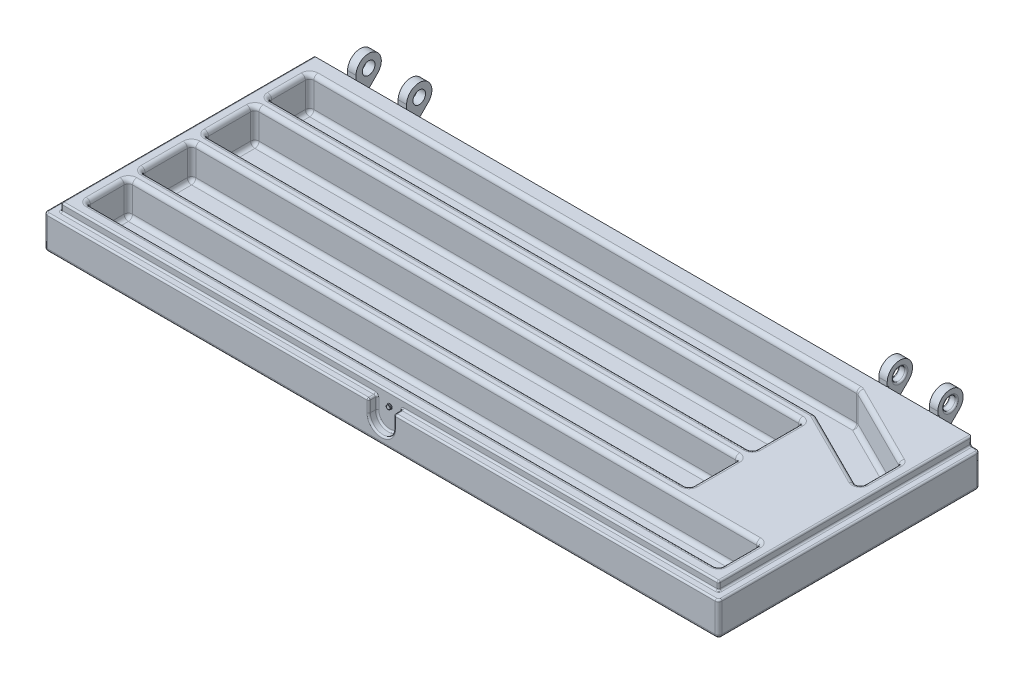
SolidWorks part; units mm, degrees
ref_plane "前视基准面" through (0, 0, 0) normal (0, 0, 1) x (1, 0, 0)
ref_plane "上视基准面" through (0, 0, 0) normal (0, 1, 0) x (1, 0, 0)
ref_plane "右视基准面" through (0, 0, 0) normal (1, 0, 0) x (0, 0, -1)
other "Configuration Table"
sketch "草图1" plane through (0, 0, 0) normal (0, 1, 0) x (1, 0, 0)
  line L1 (0, 0) -> (160, 0)
  line L2 (0, 0) -> (0, 62)
  line L3 (0, 62) -> (160, 62)
  line L4 (160, 0) -> (160, 62)
  dimension "D1" = 160
  dimension "D2" = 62
extrude "凸台-拉伸1" add sketch "草图1" along normal blind 10
sketch "草图2" plane through (0, 10, 0) normal (0, 1, 0) x (1, 0, 0)
  line L0 (5, 5) -> (5, 0) construction
  line L1 (5, 5) -> (155, 5)
  line L2 (5, 5) -> (5, 15)
  line L3 (5, 15) -> (155, 15)
  line L4 (155, 5) -> (155, 15)
  line L5 (5, 18) -> (135, 18)
  line L6 (5, 18) -> (5, 30)
  line L7 (5, 30) -> (135, 30)
  line L8 (135, 18) -> (135, 30)
  line L9 (5, 33) -> (135, 33)
  line L10 (5, 33) -> (5, 45)
  line L11 (5, 45) -> (135, 45)
  line L12 (135, 33) -> (135, 45)
  line L13 (5, 48) -> (135, 48)
  line L14 (5, 48) -> (5, 58)
  line L15 (5, 58) -> (135, 58)
  line L21 (0, 0) -> (160, 0) construction
  line L22 (5, 15) -> (5, 18) construction
  line L23 (5, 33) -> (5, 30) construction
  line L24 (5, 48) -> (5, 45) construction
  line L25 (5, 62) -> (5, 58) construction
  line L26 (160, 62) -> (0, 62) construction
  line L28 (0, 62) -> (0, 0) construction
  line L29 (160, 0) -> (160, 62) construction
  line L30 (135, 58) -> (155, 48)
  line L31 (155, 48) -> (155, 38)
  line L32 (155, 38) -> (135, 48)
  line L33 (135, 48) -> (155, 48) construction
  line L34 (135, 58) -> (135, 48) construction
  dimension "D1" = 10
  dimension "D2" = 4
  dimension "D3" = 12
  dimension "D4" = 5
  dimension "D5" = 150
  dimension "D6" = 130
  dimension "D7" = 5
  dimension "D8" = 5
  dimension "D9" = 3
  dimension "D10" = 10
  dimension "D11" = 12
extrude "切除-拉伸1" cut sketch "草图2" against normal blind 8
ref_plane "基准面1" through (150, 0, 0) normal (1, 0, 0) x (0, 0, -1)
ref_plane "基准面4" through (136, 0, 0) normal (-1, 0, 0) x (0, 0, 1)
ref_plane "基准面-对称" through (80, 0, 0) normal (1, 0, 0) x (0, 0, -1)
sketch "草图3" plane through (150, 0, 0) normal (1, 0, 0) x (0, 0, -1)
  line L0 (62, 10) -> (62, 11)
  line L1 (62, 11) -> (65, 11) construction
  line L2 (62, 3.7574) -> (67.1213, 8.8787)
  line L3 (62, 10) -> (62, 0) construction
  line L4 (62, 10) -> (62, 3.7574)
  circle A0 centre (65, 11) radius 3
  circle A1 centre (65, 11) radius 1.5
  dimension "D1" = 3
  dimension "D3" = 6
  dimension "D2" = 1
  dimension "D4" = 45
extrude "凸台-拉伸2" add sketch "草图3" against normal blind 2
sketch "草图5" plane through (136, 0, 0) normal (-1, 0, 0) x (0, 0, 1)
  line L0 (-62, 3.7574) -> (-62, 10) construction
  line L1 (-62, 10) -> (-62, 11) construction
  line L2 (-62, 3.7574) -> (-67.1213, 8.8787) construction
  line L3 (-62, 3.7574) -> (-62, 10)
  line L4 (-62, 10) -> (-62, 11)
  line L5 (-62, 3.7574) -> (-67.1213, 8.8787)
  circle A0 centre (-65, 11) radius 1.5 construction
  arc A1 (-62, 11) -> (-67.1213, 8.8787) centre (-65, 11) ccw construction
  circle A2 centre (-65, 11) radius 1.5
  arc A3 (-62, 11) -> (-67.1213, 8.8787) centre (-65, 11) ccw
extrude "凸台-拉伸3" add sketch "草图5" against normal blind 2 contours L4 A3 L5 L3 A2
mirror "镜向1" about plane through (80, 0, 0) normal (1, 0, 0) of "凸台-拉伸3", "凸台-拉伸2"
sketch "草图6" plane through (0, 10, 0) normal (0, 1, 0) x (1, 0, 0)
  line L0 (0, 62) -> (0, 0) construction
  line L1 (0, 0) -> (160, 0) construction
  line L2 (160, 0) -> (160, 62) construction
  line L3 (0, 62) -> (0, 0)
  line L4 (0, 0) -> (160, 0)
  line L5 (160, 0) -> (160, 62)
  line L6 (0, 62) -> (2, 62)
  line L7 (10, 62) -> (0, 62) construction
  line L8 (2, 62) -> (2, 2)
  line L9 (2, 2) -> (158, 2)
  line L10 (158, 2) -> (158, 62)
  line L11 (160, 62) -> (150, 62) construction
  line L12 (158, 62) -> (160, 62)
  dimension "D1" = 2
  dimension "D2" = 2
extrude "切除-拉伸2" cut sketch "草图6" against normal blind 2
sketch "草图7" plane through (0, 0, 0) normal (0, 0, 1) x (1, 0, 0)
  line L0 (80, 8) -> (80, 5) construction
  line L1 (0, 8) -> (160, 8) construction
  line L2 (83, 5) -> (83, 8)
  line L3 (77, 5) -> (77, 8)
  line L4 (77, 8) -> (83, 8)
  arc A0 (77, 5) -> (83, 5) centre (80, 5) ccw
  dimension "D2" = 3
  dimension "D1" = 3
extrude "切除-拉伸3" cut sketch "草图7" against normal up to surface (2 mm away) up to face at (80, 9, -2)
sketch "草图8" plane through (0, 0, -2) normal (0, 0, 1) x (1, 0, 0)
  line L0 (80, 5) -> (80, 7) construction
  circle A0 centre (80, 7) radius 0.5
  dimension "D1" = 1
  dimension "D2" = 2
extrude "凸台-拉伸4" add sketch "草图8" along normal blind 0.4
fillet "圆角1" radius 0.8 8 edges at (80, 0, 0) (160, 0, -31) (80, 0, -62) (0, 0, -31) (0, 4, 0) (0, 4, -62) (160, 4, 0) (160, 4, -62)
fillet "圆角2" radius 0.4 39 edges at (158, 9, -62) (2, 9, -62) (77, 6.5, 0) (77, 6.5, -2) (83, 6.5, 0) (83, 6.5, -2) (136, 11, -63.5) (138, 11, -63.5) (148, 11, -66.5) (150, 11, -66.5) (80, 2, 0) (80, 2, -2) (83, 8, -1) (120.5, 8, -2) (158, 8, -32) (158.6, 8, -62) (159.7657, 8, -61.7657) (160, 8, -31) (159.7657, 8, -0.2343) (121.1, 8, 0) (0.2343, 8, -61.7657) (1.4, 8, -62) (2, 8, -32) (39.5, 8, -2) (77, 8, -1) (38.9, 8, 0) (0.2343, 8, -0.2343) (0, 8, -31) (136, 6.8787, -62) (137, 3.7574, -62) (138, 6.8787, -62) (149, 3.7574, -62) (148, 6.8787, -62) (150, 6.8787, -62) (158, 9, -2) (2, 9, -2) (2, 10, -32) (80, 10, -2) (158, 10, -32)
fillet "圆角3" radius 1 54 edges at (80, 10, -5) (80, 10, -15) (70, 10, -18) (70, 10, -30) (70, 10, -33) (70, 10, -45) (5, 10, -53) (145, 10, -43) (145, 10, -53) (5, 6, -45) (5, 6, -33) (5, 10, -39) (5, 6, -30) (5, 6, -18) (5, 10, -24) (5, 6, -15) (5, 6, -5) (5, 10, -10) (80, 2, -15) (80, 2, -5) (5, 2, -10) (155, 6, -5) (155, 2, -10) (155, 6, -15) (155, 10, -10) (70, 2, -30) (70, 2, -18) (5, 2, -24) (135, 6, -18) (135, 2, -24) (135, 6, -30) (135, 10, -24) (70, 2, -45) (70, 2, -33) (5, 2, -39) (135, 6, -33) (135, 2, -39) (135, 6, -45) (135, 10, -39) (5, 6, -48) (135, 6, -48) (70, 10, -48) (135, 6, -58) (5, 6, -58) (70, 10, -58) (155, 6, -38) (155, 6, -48) (155, 10, -43) (70, 2, -58) (145, 2, -53) (155, 2, -43) (145, 2, -43) (70, 2, -48) (5, 2, -53)
fillet "圆角4" radius 0.1 2 edges at (79.5, 7, -2) (80.5, 7, -1.6)
